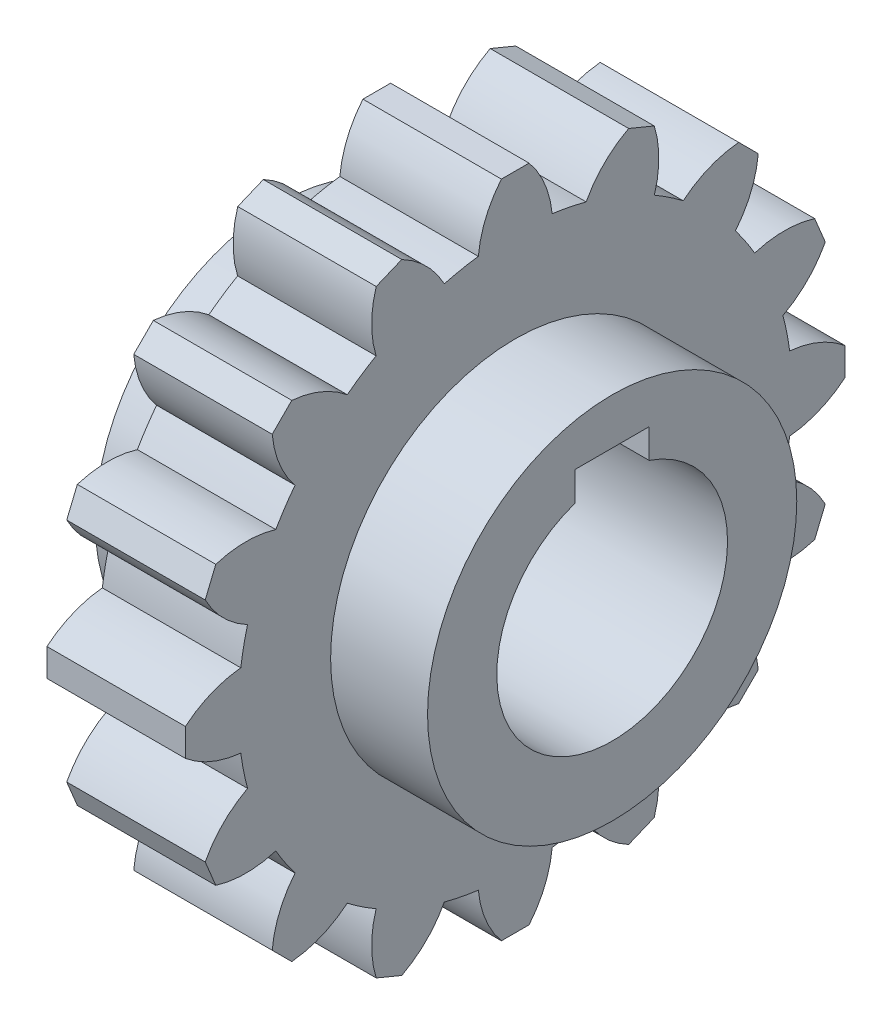
SolidWorks part; units mm, degrees
ref_plane "Front Plane" through (0, 0, 0) normal (0, 0, 1) x (1, 0, 0)
ref_plane "Top Plane" through (0, 0, 0) normal (0, 1, 0) x (1, 0, 0)
ref_plane "Right Plane" through (0, 0, 0) normal (1, 0, 0) x (0, 0, -1)
sketch "Sketch1" plane through (0, 0, 0) normal (1, 0, 0) x (0, 0, -1)
  circle A0 centre (0, 0) radius 30
  dimension "D1" = 60
extrude "Boss-Extrude1" add sketch "Sketch1" along normal mid plane 15
sketch "Sketch3" plane through (7.5, 0, 0) normal (1, 0, 0) x (0, 0, -1)
  line L0 (0, 0) -> (0, 35.7321) construction
  line L1 (-1.5, 35.7321) -> (1.5, 35.7321)
  arc A0 (-4, 29.7321) -> (4, 29.7321) centre (0, 0) cw
  circle A2 centre (0, 0) radius 30 construction
  arc A3 (-1.5, 35.7321) -> (-4, 29.7321) centre (6.9505, 28.6902) ccw
  arc A4 (1.5, 35.7321) -> (4, 29.7321) centre (-6.9505, 28.6902) cw
  point P9 (0, 30)
  point P12 (0, 0)
  dimension "D3" = 6
  dimension "D4" = 11
  dimension "D1" = 1.5
  dimension "D2" = 4
extrude "Boss-Extrude2" add sketch "Sketch3" against normal up to surface (15 mm away) contours A4 A0 A3 L1 up to face at (-7.5, 0, -30)
sketch "Sketch4" plane through (0, 0, 0) normal (1, 0, 0) x (0, 0, -1)
  circle A0 centre (0, 0) radius 20
  dimension "D1" = 40
extrude "Boss-Extrude3" add sketch "Sketch4" along normal mid plane 36
sketch "Sketch5" plane through (18, 0, 0) normal (1, 0, 0) x (0, 0, -1)
  line L0 (0, 0) -> (0, 15) construction
  line L1 (-4, 15) -> (4, 15)
  line L2 (-4, 15) -> (-4, 11.8427)
  line L3 (4, 15) -> (4, 11.8427)
  arc A0 (-4, 11.8427) -> (4, 11.8427) centre (0, 0) ccw
  dimension "D1" = 25
  dimension "D2" = 8
  dimension "D3" = 15
extrude "Cut-Extrude1" cut sketch "Sketch5" against normal through all
pattern_circular "CirPattern1" count 16 over 360 about axis through (0, 0, 0) along (1, 0, 0) of "Boss-Extrude2"
